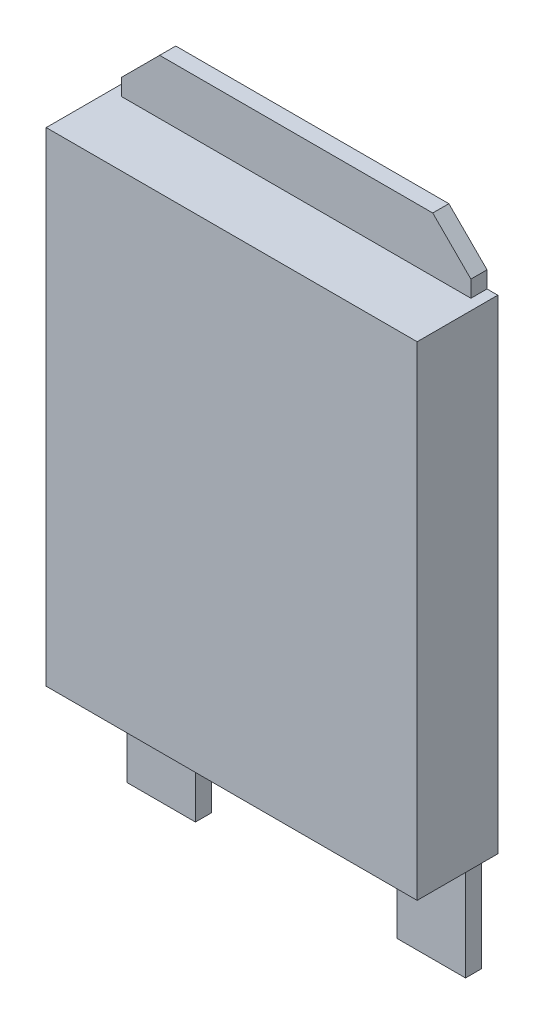
SolidWorks part; units mm, degrees
ref_plane "Front Plane" through (0, 0, 0) normal (0, 0, 1) x (1, 0, 0)
ref_plane "Top Plane" through (0, 0, 0) normal (0, 1, 0) x (1, 0, 0)
ref_plane "Right Plane" through (0, 0, 0) normal (1, 0, 0) x (0, 0, -1)
sketch "Sketch1" plane through (0, 0, 0) normal (0, 0, 1) x (1, 0, 0)
  line L1 (-3.45, 4.5) -> (3.45, 4.5)
  line L2 (-3.45, 4.5) -> (-3.45, -4.5)
  line L3 (-3.45, -4.5) -> (3.45, -4.5)
  line L4 (3.45, 4.5) -> (3.45, -4.5)
  line L5 (-3.45, 4.5) -> (3.45, -4.5) construction
  line L6 (-3.45, -4.5) -> (3.45, 4.5) construction
  point P0 (0, 0)
  dimension "D1" = 9
  dimension "D2" = 6.9
extrude "Boss-Extrude1" add sketch "Sketch1" along normal blind 1.5
sketch "Sketch2" plane through (0, 0, 0) normal (0, 0, 1) x (1, 0, 0)
  line L0 (3.25, 4.5) -> (3.25, 4.8089)
  line L1 (3.45, 4.5) -> (-3.45, 4.5) construction
  line L2 (2.54, 5.5189) -> (-2.54, 5.5189)
  line L3 (-3.25, 4.8089) -> (-3.25, 4.5)
  line L4 (3.25, 4.8089) -> (2.54, 5.5189)
  line L5 (-2.54, 5.5189) -> (-3.25, 4.8089)
  line L6 (3.15, -4.5) -> (3.15, -6.5)
  line L7 (-3.45, -4.5) -> (3.45, -4.5) construction
  line L8 (3.15, -6.5) -> (1.8738, -6.5)
  line L9 (1.8738, -6.5) -> (1.8738, -4.5)
  line L10 (3.25, 4.5) -> (-3.25, 4.5)
  line L11 (-3.15, -6.5) -> (-1.8738, -6.5)
  line L12 (-3.15, -4.5) -> (-3.15, -6.5)
  line L13 (-1.8738, -6.5) -> (-1.8738, -4.5)
  line L14 (3.15, -4.5) -> (1.8738, -4.5)
  line L15 (-1.8738, -4.5) -> (-3.15, -4.5)
  point P1 (3.25, 5.5189)
  point P5 (-3.25, 5.5189)
  dimension "D1" = 0.2
  dimension "D2" = 0.2
  dimension "D3" = 0.3
  dimension "D4" = 2
extrude "Boss-Extrude2" add sketch "Sketch2" along normal blind 0.3
